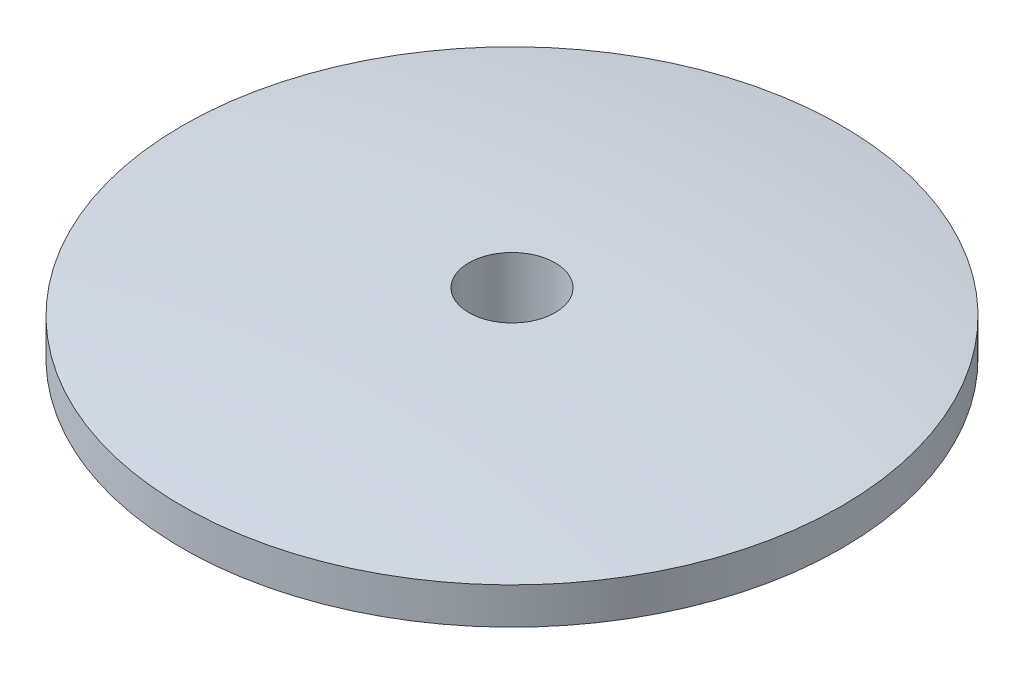
SolidWorks part; units mm, degrees
ref_plane "Alzado" through (0, 0, 0) normal (0, 0, 1) x (1, 0, 0)
ref_plane "Planta" through (0, 0, 0) normal (0, 1, 0) x (1, 0, 0)
ref_plane "Vista lateral" through (0, 0, 0) normal (1, 0, 0) x (0, 0, -1)
sketch "Sketch1" plane through (0, 0, 0) normal (0, 0, 1) x (1, 0, 0)
  line L0 (0, -203.3422) -> (0, 9963.7678) construction
  line L1 (-203.3422, 0) -> (9963.7678, 0) construction
  line L2 (-203.6167, 0.0895) -> (9963.4933, 0.0895) construction
  line L3 (0.1055, -203.3759) -> (0.1055, 9963.7341) construction
  line L4 (0.8051, -203.3957) -> (0.8051, 9963.7143) construction
  line L5 (0.1055, 0.149) -> (0.1055, 0)
  line L6 (0.1055, 0) -> (0.8051, 0)
  line L7 (0.8051, 0) -> (0.8051, 0.0895)
  arc A0 (0.8051, 0.0895) -> (0.1055, 0.149) centre (0, -5.2361) ccw
  point P10 (0.8051, 0.0895)
  dimension "D5" = 5.3861
  dimension "D1" = 0.1055
  dimension "D2" = 0.8051
  dimension "D3" = 0.0895
revolve "Revolve1" add sketch "Sketch1" angle 360 about L0
